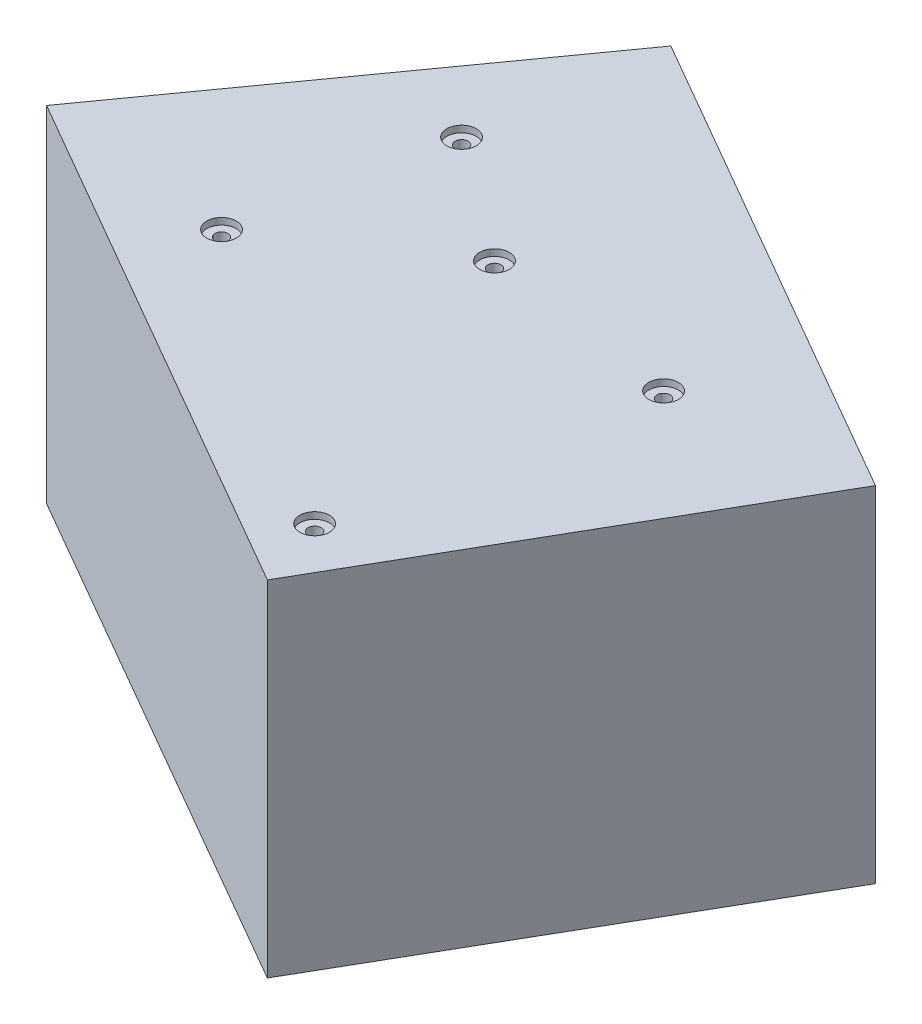
SolidWorks part; units mm, degrees
ref_plane "Front Plane" through (0, 0, 0) normal (0, 0, 1) x (1, 0, 0)
ref_plane "Top Plane" through (0, 0, 0) normal (0, 1, 0) x (1, 0, 0)
ref_plane "Right Plane" through (0, 0, 0) normal (1, 0, 0) x (0, 0, -1)
sketch "Sketch1" plane through (0, 0, 0) normal (0, 1, 0) x (1, 0, 0)
  line L0 (-38.4791, 14.0479) -> (17.4683, -18.2012)
  line L1 (17.4683, -18.2012) -> (20.5411, -12.8703)
  line L2 (41.3321, 23.1989) -> (17.4683, -18.2012)
  line L3 (41.3321, 23.1989) -> (-10.5054, 53.0791)
  line L4 (-10.5054, 53.0791) -> (-38.4791, 14.0479)
extrude "Boss-Extrude1" add sketch "Sketch1" along normal blind 37 contours L3 L4 L0 L1 L2
hole_wizard "CBORE for #00 Binding Head Machine Screw1" positions "Sketch4" profile "Sketch5" counterbore size "#00" standard "ANSI Inch" end condition through all
sketch "Sketch4" plane through (0, 37, 0) normal (0, 1, 0) x (1, 0, 0)
  point P0 (14.7823, -10.4421)
  point P2 (0, 23.6417)
  point P4 (21.1629, 20.6303)
  point P6 (-17.5586, 11.9071)
  point P8 (-13.2543, 33.3668)
sketch "Sketch5" plane through (14.7823, 37, 10.4421) normal (1, 0, 0) x (0, 0, 1)
  line L0 (0, 0) -> (0, 37)
  line L1 (0, 37) -> (0.6985, 37)
  line L3 (0.6985, 37) -> (0.6985, 0.7112)
  line L4 (0.6985, 0.7112) -> (1.5875, 0.7112)
  line L5 (1.5875, 0.7112) -> (1.5875, 0)
  line L7 (1.5875, 0) -> (0, 0)
  line L11 (0, -6.35) -> (0, 107.95) construction
  dimension "Thru Hole Dia." = 1.397
  dimension "Thru Hole Depth" = 37
  dimension "C'Bore Dia." = 3.175
  dimension "C'Bore Depth" = 0.7112
